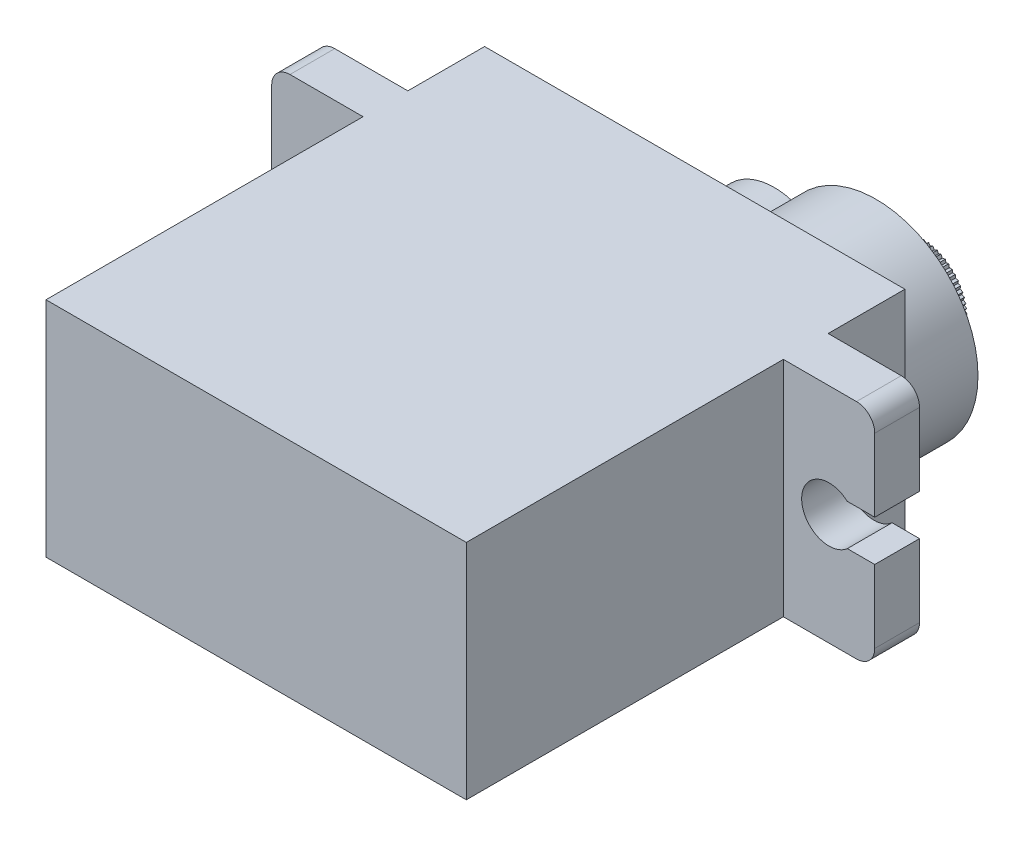
SolidWorks part; units mm, degrees
other "İşaretleme1"
sketch "Çizim23" plane through (16.5, -6.05, -13.15) normal (0.0047, -0.3236, -0.9462) x (-0.9915, -0.1242, 0.0376)
ref_plane "Ön Düzlem" through (0, 0, 0) normal (0, 0, 1) x (1, 0, 0)
ref_plane "Üst Düzlem" through (0, 0, 0) normal (0, 1, 0) x (1, 0, 0)
ref_plane "Sağ Düzlem" through (0, 0, 0) normal (1, 0, 0) x (0, 0, -1)
sketch "Çizim1" plane through (0, 0, 0) normal (0, 0, 1) x (1, 0, 0)
  line L1 (-11.5, -6.1) -> (11.5, -6.1)
  line L2 (-11.5, -6.1) -> (-11.5, 6.1)
  line L3 (-11.5, 6.1) -> (11.5, 6.1)
  line L4 (11.5, -6.1) -> (11.5, 6.1)
  line L5 (-11.5, -6.1) -> (11.5, 6.1) construction
  line L6 (-11.5, 6.1) -> (11.5, -6.1) construction
  point P0 (0, 0)
  dimension "D1" = 23
  dimension "D2" = 12.2
extrude "Yükseklik-Ekstrüzyon1" add sketch "Çizim1" along normal blind 17.35
sketch "Çizim4" plane through (11.5, 0, 0) normal (1, 0, 0) x (0, 0, -1)
  line L0 (-17.35, -6.1) -> (0, -6.1) construction
  line L1 (0, 6.1) -> (2.45, 6.1)
  line L2 (0, 6.1) -> (0, -6.1)
  line L3 (0, -6.1) -> (2.45, -6.1)
  line L4 (2.45, 6.1) -> (2.45, -6.1)
  dimension "D1" = 2.45
extrude "Yükseklik-Ekstrüzyon2" add sketch "Çizim4" along normal blind 5
sketch "Çizim5" plane through (-11.5, 0, 0) normal (-1, 0, 0) x (0, 0, 1)
  line L0 (17.35, 6.1) -> (0, 6.1) construction
  line L1 (0, -6.1) -> (-2.45, -6.1)
  line L2 (0, -6.1) -> (0, 6.1)
  line L3 (0, 6.1) -> (-2.45, 6.1)
  line L4 (-2.45, -6.1) -> (-2.45, 6.1)
  dimension "D1" = 2.45
extrude "Yükseklik-Ekstrüzyon3" add sketch "Çizim5" along normal blind 5
sketch "Çizim6" plane through (16.5, 0, 0) normal (1, 0, 0) x (0, 0, -1)
  line L0 (0, 0) -> (2.45, 0) construction
  line L1 (0, 6.1) -> (0, -6.1) construction
  line L2 (2.45, -6.1) -> (2.45, 6.1) construction
  line L4 (2.45, 1.12) -> (0, 1.12)
  line L5 (2.45, 1.12) -> (2.45, -1.12)
  line L6 (2.45, -1.12) -> (0, -1.12)
  line L7 (0, 1.12) -> (0, -1.12)
  line L8 (2.45, 1.12) -> (0, -1.12) construction
  line L9 (2.45, -1.12) -> (0, 1.12) construction
  point P6 (1.225, 0)
  dimension "D1" = 2.24
sketch "Çizim7" plane through (0, 0, 0) normal (0, 0, -1) x (-1, 0, 0)
  line L0 (-11.5, 6.1) -> (11.5, 6.1) construction
  line L1 (-11.5, -6.1) -> (11.5, -6.1)
  line L2 (-11.5, -6.1) -> (-11.5, 6.1)
  line L3 (-11.5, 6.1) -> (11.5, 6.1)
  line L4 (11.5, -6.1) -> (11.5, 6.1)
  line L5 (-11.5, -6.1) -> (11.5, 6.1) construction
  line L6 (-11.5, 6.1) -> (11.5, -6.1) construction
  point P0 (0, 0)
  dimension "D1" = 23
extrude "Yükseklik-Ekstrüzyon4" add sketch "Çizim7" along normal blind 6.65
sketch "Çizim8" plane through (0, 0, -2.45) normal (0, 0, -1) x (-1, 0, 0)
  line L0 (0, 0.2404) -> (0, 3.5063) construction
  circle A0 centre (-14, 0) radius 1.5
  circle A1 centre (14, 0) radius 1.5
  dimension "D2" = 3
  dimension "D1" = 2.5
extrude "Kes-Ekstrüzyon1" cut sketch "Çizim8" against normal up to surface (2.45 mm away) up to face at (14, 0, 0)
fillet "Radyus1" radius 1 4 edges at (-16.5, 6.1, -1.225) (-16.5, -6.1, -1.225) (16.5, -6.1, -1.225) (16.5, 6.1, -1.225)
extrude "Kes-Ekstrüzyon2" cut sketch "Çizim6" against normal up to surface (1.5022 mm away)
sketch "Çizim9" plane through (-16.5, 0, 0) normal (-1, 0, 0) x (0, 0, 1)
  line L0 (0, 0) -> (-2.45, 0) construction
  line L1 (-2.45, 6.1) -> (-2.45, -6.1) construction
  line L2 (0, -6.1) -> (0, 6.1) construction
  line L3 (-2.45, -1.12) -> (0, -1.12)
  line L4 (-2.45, -1.12) -> (-2.45, 1.12)
  line L5 (-2.45, 1.12) -> (0, 1.12)
  line L6 (0, -1.12) -> (0, 1.12)
  line L7 (-2.45, -1.12) -> (0, 1.12) construction
  line L8 (-2.45, 1.12) -> (0, -1.12) construction
  point P5 (-1.225, 0)
  dimension "D1" = 2.24
extrude "Kes-Ekstrüzyon3" cut sketch "Çizim9" against normal up to surface (1.5022 mm away)
sketch "Çizim10" plane through (0, 0, -6.65) normal (0, 0, -1) x (-1, 0, 0)
  line L0 (-11.5, 0) -> (-5.925, 0) construction
  line L1 (-11.5, 6.1) -> (-11.5, -6.1) construction
  circle A0 centre (-5.925, 0) radius 5.575
  dimension "D2" = 11.15
  dimension "D1" = 5.575
extrude "Yükseklik-Ekstrüzyon5" add sketch "Çizim10" along normal blind 4
sketch "Çizim11" plane through (0, 0, -10.65) normal (0, 0, -1) x (-1, 0, 0)
  circle A0 centre (-5.925, 0) radius 2.5
  dimension "D1" = 5
extrude "Yükseklik-Ekstrüzyon6" add sketch "Çizim11" along normal blind 2.5
sketch "Çizim12" plane through (0, 0, -6.65) normal (0, 0, -1) x (-1, 0, 0)
  line L0 (-0.35, 0) -> (3, 0) construction
  circle A0 centre (-5.925, 0) radius 5.575 construction
  circle A1 centre (-5.925, 0) radius 5.575 construction
  circle A2 centre (-0.35, 0) radius 3.35
  dimension "D1" = 3.35
extrude "Yükseklik-Ekstrüzyon7" add sketch "Çizim12" along normal blind 4
sketch "Çizim13" plane through (0, 0, -13.15) normal (0, 0, -1) x (-1, 0, 0)
  line L0 (-5.925, 2.375) -> (-5.815, 2.485)
  line L1 (-5.925, 2.375) -> (-6.035, 2.485)
  line L2 (-6.035, 2.485) -> (-6.1562, 2.3637)
  line L3 (-5.815, 2.485) -> (-5.6938, 2.3637)
  line L4 (-5.5481, 2.4587) -> (-5.6906, 2.3634)
  line L5 (-5.4617, 2.3294) -> (-5.5481, 2.4587)
  line L6 (-5.4617, 2.3294) -> (-5.3324, 2.4158)
  line L7 (-5.3324, 2.4158) -> (-5.2371, 2.2732)
  line L8 (-5.0756, 2.3379) -> (-5.234, 2.2723)
  line L9 (-5.0161, 2.1942) -> (-5.0756, 2.3379)
  line L10 (-5.0161, 2.1942) -> (-4.8725, 2.2537)
  line L11 (-4.8725, 2.2537) -> (-4.8068, 2.0953)
  line L12 (-4.6359, 2.1273) -> (-4.804, 2.0938)
  line L13 (-4.6055, 1.9747) -> (-4.6359, 2.1273)
  line L14 (-4.6055, 1.9747) -> (-4.453, 2.0051)
  line L15 (-4.453, 2.0051) -> (-4.4196, 1.8369)
  line L16 (-4.2456, 1.8349) -> (-4.4171, 1.8349)
  line L17 (-4.2456, 1.6794) -> (-4.2456, 1.8349)
  line L18 (-4.2456, 1.6794) -> (-4.0901, 1.6794)
  line L19 (-4.0901, 1.6794) -> (-4.0901, 1.5079)
  line L20 (-3.9199, 1.472) -> (-4.0881, 1.5054)
  line L21 (-3.9503, 1.3195) -> (-3.9199, 1.472)
  line L22 (-3.9503, 1.3195) -> (-3.7977, 1.2891)
  line L23 (-3.7977, 1.2891) -> (-3.8312, 1.121)
  line L24 (-3.6713, 1.0525) -> (-3.8297, 1.1182)
  line L25 (-3.7308, 0.9089) -> (-3.6713, 1.0525)
  line L26 (-3.7308, 0.9089) -> (-3.5871, 0.8494)
  line L27 (-3.5871, 0.8494) -> (-3.6527, 0.691)
  line L28 (-3.5092, 0.5926) -> (-3.6518, 0.6879)
  line L29 (-3.5956, 0.4633) -> (-3.5092, 0.5926)
  line L30 (-3.5956, 0.4633) -> (-3.4663, 0.3769)
  line L31 (-3.4663, 0.3769) -> (-3.5616, 0.2344)
  line L32 (-3.44, 0.11) -> (-3.5613, 0.2312)
  line L33 (-3.55, 0) -> (-3.44, 0.11)
  line L34 (-3.55, 0) -> (-3.44, -0.11)
  line L35 (-3.44, -0.11) -> (-3.5613, -0.2312)
  line L36 (-3.4663, -0.3769) -> (-3.5616, -0.2344)
  line L37 (-3.5956, -0.4633) -> (-3.4663, -0.3769)
  line L38 (-3.5956, -0.4633) -> (-3.5092, -0.5926)
  line L39 (-3.5092, -0.5926) -> (-3.6518, -0.6879)
  line L40 (-3.5871, -0.8494) -> (-3.6527, -0.691)
  line L41 (-3.7308, -0.9089) -> (-3.5871, -0.8494)
  line L42 (-3.7308, -0.9089) -> (-3.6713, -1.0525)
  line L43 (-3.6713, -1.0525) -> (-3.8297, -1.1182)
  line L44 (-3.7977, -1.2891) -> (-3.8312, -1.121)
  line L45 (-3.9503, -1.3195) -> (-3.7977, -1.2891)
  line L46 (-3.9503, -1.3195) -> (-3.9199, -1.472)
  line L47 (-3.9199, -1.472) -> (-4.0881, -1.5054)
  line L48 (-4.0901, -1.6794) -> (-4.0901, -1.5079)
  line L49 (-4.2456, -1.6794) -> (-4.0901, -1.6794)
  line L50 (-4.2456, -1.6794) -> (-4.2456, -1.8349)
  line L51 (-4.2456, -1.8349) -> (-4.4171, -1.8349)
  line L52 (-4.453, -2.0051) -> (-4.4196, -1.8369)
  line L53 (-4.6055, -1.9747) -> (-4.453, -2.0051)
  line L54 (-4.6055, -1.9747) -> (-4.6359, -2.1273)
  line L55 (-4.6359, -2.1273) -> (-4.804, -2.0938)
  line L56 (-4.8725, -2.2537) -> (-4.8068, -2.0953)
  line L57 (-5.0161, -2.1942) -> (-4.8725, -2.2537)
  line L58 (-5.0161, -2.1942) -> (-5.0756, -2.3379)
  line L59 (-5.0756, -2.3379) -> (-5.234, -2.2723)
  line L60 (-5.3324, -2.4158) -> (-5.2371, -2.2732)
  line L61 (-5.4617, -2.3294) -> (-5.3324, -2.4158)
  line L62 (-5.4617, -2.3294) -> (-5.5481, -2.4587)
  line L63 (-5.5481, -2.4587) -> (-5.6906, -2.3634)
  line L64 (-5.815, -2.485) -> (-5.6938, -2.3637)
  line L65 (-5.925, -2.375) -> (-5.815, -2.485)
  line L66 (-5.925, -2.375) -> (-6.035, -2.485)
  line L67 (-6.035, -2.485) -> (-6.1562, -2.3637)
  line L68 (-6.3019, -2.4587) -> (-6.1594, -2.3634)
  line L69 (-6.3883, -2.3294) -> (-6.3019, -2.4587)
  line L70 (-6.3883, -2.3294) -> (-6.5176, -2.4158)
  line L71 (-6.5176, -2.4158) -> (-6.6129, -2.2732)
  line L72 (-6.7744, -2.3379) -> (-6.616, -2.2723)
  line L73 (-6.8339, -2.1942) -> (-6.7744, -2.3379)
  line L74 (-6.8339, -2.1942) -> (-6.9775, -2.2537)
  line L75 (-6.9775, -2.2537) -> (-7.0432, -2.0953)
  line L76 (-7.2141, -2.1273) -> (-7.046, -2.0938)
  line L77 (-7.2445, -1.9747) -> (-7.2141, -2.1273)
  line L78 (-7.2445, -1.9747) -> (-7.397, -2.0051)
  line L79 (-7.397, -2.0051) -> (-7.4304, -1.8369)
  line L80 (-7.6044, -1.8349) -> (-7.4329, -1.8349)
  line L81 (-7.6044, -1.6794) -> (-7.6044, -1.8349)
  line L82 (-7.6044, -1.6794) -> (-7.7599, -1.6794)
  line L83 (-7.7599, -1.6794) -> (-7.7599, -1.5079)
  line L84 (-7.9301, -1.472) -> (-7.7619, -1.5054)
  line L85 (-7.8997, -1.3195) -> (-7.9301, -1.472)
  line L86 (-7.8997, -1.3195) -> (-8.0523, -1.2891)
  line L87 (-8.0523, -1.2891) -> (-8.0188, -1.121)
  line L88 (-8.1787, -1.0525) -> (-8.0203, -1.1182)
  line L89 (-8.1192, -0.9089) -> (-8.1787, -1.0525)
  line L90 (-8.1192, -0.9089) -> (-8.2629, -0.8494)
  line L91 (-8.2629, -0.8494) -> (-8.1973, -0.691)
  line L92 (-8.3408, -0.5926) -> (-8.1982, -0.6879)
  line L93 (-8.2544, -0.4633) -> (-8.3408, -0.5926)
  line L94 (-8.2544, -0.4633) -> (-8.3837, -0.3769)
  line L95 (-8.3837, -0.3769) -> (-8.2884, -0.2344)
  line L96 (-8.41, -0.11) -> (-8.2887, -0.2312)
  line L97 (-8.3, 0) -> (-8.41, -0.11)
  line L98 (-8.3, 0) -> (-8.41, 0.11)
  line L99 (-8.41, 0.11) -> (-8.2887, 0.2312)
  line L100 (-8.3837, 0.3769) -> (-8.2884, 0.2344)
  line L101 (-8.2544, 0.4633) -> (-8.3837, 0.3769)
  line L102 (-8.2544, 0.4633) -> (-8.3408, 0.5926)
  line L103 (-8.3408, 0.5926) -> (-8.1982, 0.6879)
  line L104 (-8.2629, 0.8494) -> (-8.1973, 0.691)
  line L105 (-8.1192, 0.9089) -> (-8.2629, 0.8494)
  line L106 (-8.1192, 0.9089) -> (-8.1787, 1.0525)
  line L107 (-8.1787, 1.0525) -> (-8.0203, 1.1182)
  line L108 (-8.0523, 1.2891) -> (-8.0188, 1.121)
  line L109 (-7.8997, 1.3195) -> (-8.0523, 1.2891)
  line L110 (-7.8997, 1.3195) -> (-7.9301, 1.472)
  line L111 (-7.9301, 1.472) -> (-7.7619, 1.5054)
  line L112 (-7.7599, 1.6794) -> (-7.7599, 1.5079)
  line L113 (-7.6044, 1.6794) -> (-7.7599, 1.6794)
  line L114 (-7.6044, 1.6794) -> (-7.6044, 1.8349)
  line L115 (-7.6044, 1.8349) -> (-7.4329, 1.8349)
  line L116 (-7.397, 2.0051) -> (-7.4304, 1.8369)
  line L117 (-7.2445, 1.9747) -> (-7.397, 2.0051)
  line L118 (-7.2445, 1.9747) -> (-7.2141, 2.1273)
  line L119 (-7.2141, 2.1273) -> (-7.046, 2.0938)
  line L120 (-6.9775, 2.2537) -> (-7.0432, 2.0953)
  line L121 (-6.8339, 2.1942) -> (-6.9775, 2.2537)
  line L122 (-6.8339, 2.1942) -> (-6.7744, 2.3379)
  line L123 (-6.7744, 2.3379) -> (-6.616, 2.2723)
  line L124 (-6.5176, 2.4158) -> (-6.6129, 2.2732)
  line L125 (-6.3883, 2.3294) -> (-6.5176, 2.4158)
  line L126 (-6.3883, 2.3294) -> (-6.3019, 2.4587)
  line L127 (-6.3019, 2.4587) -> (-6.1594, 2.3634)
  line L128 (-8.1973, 0.691) -> (-8.1982, 0.6879)
  line L129 (-8.0188, 1.121) -> (-8.0203, 1.1182)
  line L130 (-7.7599, 1.5079) -> (-7.7619, 1.5054)
  line L131 (-7.4304, 1.8369) -> (-7.4329, 1.8349)
  line L132 (-7.0432, 2.0953) -> (-7.046, 2.0938)
  line L133 (-6.6129, 2.2732) -> (-6.616, 2.2723)
  line L134 (-6.1562, 2.3637) -> (-6.1594, 2.3634)
  line L135 (-5.6906, 2.3634) -> (-5.6938, 2.3637)
  line L136 (-5.234, 2.2723) -> (-5.2371, 2.2732)
  line L137 (-4.804, 2.0938) -> (-4.8068, 2.0953)
  line L138 (-4.4171, 1.8349) -> (-4.4196, 1.8369)
  line L139 (-4.0881, 1.5054) -> (-4.0901, 1.5079)
  line L140 (-3.8297, 1.1182) -> (-3.8312, 1.121)
  line L141 (-3.6518, 0.6879) -> (-3.6527, 0.691)
  line L142 (-3.5613, 0.2312) -> (-3.5616, 0.2344)
  line L143 (-3.5616, -0.2344) -> (-3.5613, -0.2312)
  line L144 (-3.6527, -0.691) -> (-3.6518, -0.6879)
  line L145 (-3.8312, -1.121) -> (-3.8297, -1.1182)
  line L146 (-4.0901, -1.5079) -> (-4.0881, -1.5054)
  line L147 (-4.4196, -1.8369) -> (-4.4171, -1.8349)
  line L148 (-4.8068, -2.0953) -> (-4.804, -2.0938)
  line L149 (-5.2371, -2.2732) -> (-5.234, -2.2723)
  line L150 (-5.6938, -2.3637) -> (-5.6906, -2.3634)
  line L151 (-6.1594, -2.3634) -> (-6.1562, -2.3637)
  line L152 (-6.616, -2.2723) -> (-6.6129, -2.2732)
  line L153 (-7.046, -2.0938) -> (-7.0432, -2.0953)
  line L154 (-7.4329, -1.8349) -> (-7.4304, -1.8369)
  line L155 (-7.7619, -1.5054) -> (-7.7599, -1.5079)
  line L156 (-8.0203, -1.1182) -> (-8.0188, -1.121)
  line L157 (-8.1982, -0.6879) -> (-8.1973, -0.691)
  line L158 (-8.2887, -0.2312) -> (-8.2884, -0.2344)
  line L159 (-8.2884, 0.2344) -> (-8.2887, 0.2312)
  circle A1 centre (-5.925, 0) radius 2.5
  point P167 (-5.925, 0)
  point P229 (-5.925, 0)
  dimension "D1" = 32
  dimension "D2" = 32
extrude "Kes-Ekstrüzyon4" cut sketch "Çizim13" against normal up to surface (2.5 mm away) up to face at (3.425, 0, -10.65)
sketch "Çizim14" plane through (0, 0, -13.15) normal (0, 0, -1) x (-1, 0, 0)
  line L0 (-11.5, 0) -> (-5.925, 0) construction
  line L1 (-11.5, -6.1) -> (-11.5, 6.1) construction
  circle A0 centre (-5.925, 0) radius 0.75
  dimension "D1" = 1.5
extrude "Kes-Ekstrüzyon5" cut sketch "Çizim14" against normal blind 1
sketch "Çizim15" plane through (0, -6.1, 0) normal (0, -1, 0) x (1, 0, 0)
  line L0 (0, 17.35) -> (0, 15.35) construction
  line L1 (-11.5, 17.35) -> (11.5, 17.35) construction
  line L2 (-11.5, 8.675) -> (-9.5, 8.675) construction
  line L3 (-11.5, 17.35) -> (-11.5, 0) construction
  line L4 (11.5, 17.35) -> (11.5, 0) construction
  line L5 (-9.5, 15.35) -> (9.5, 15.35)
  line L6 (-9.5, 15.35) -> (-9.5, 2)
  line L7 (-9.5, 2) -> (9.5, 2)
  line L8 (9.5, 15.35) -> (9.5, 2)
  dimension "D1" = 2
  dimension "D2" = 2
  dimension "D3" = 2
  dimension "D4" = 2
  dimension "D5" = 2
extrude "Yükseklik-Ekstrüzyon8" add sketch "Çizim15" along normal blind 0.1
sketch "Çizim17" plane through (0, -6.2, 0) normal (0, -1, 0) x (1, 0, 0)
  line L0 (-9.5, 8.675) -> (9.5, 8.675) construction
  line L1 (-9.5, 15.35) -> (-9.5, 2) construction
  line L2 (9.5, 2) -> (9.5, 15.35) construction
  line L4 (-9.5, 6.925) -> (9.5, 6.925)
  line L5 (-9.5, 6.925) -> (-9.5, 10.425)
  line L6 (-9.5, 10.425) -> (9.5, 10.425)
  line L7 (9.5, 6.925) -> (9.5, 10.425)
  line L8 (-9.5, 6.925) -> (9.5, 10.425) construction
  line L9 (-9.5, 10.425) -> (9.5, 6.925) construction
  point P6 (0, 8.675)
  dimension "D1" = 3.5
extrude "Yükseklik-Ekstrüzyon9" add sketch "Çizim17" along normal blind 0.05
sketch "Çizim18" plane through (0, -6.25, 0) normal (0, -1, 0) x (1, 0, 0)
  line L0 (-9.5, 9.425) -> (9.5, 9.425) construction
  line L2 (9.5, 6.925) -> (9.5, 10.425) construction
  line L3 (9.5, 9.425) -> (9.5, 10.425) construction
  line L4 (9.5, 2) -> (9.5, 15.35) construction
  line L7 (-9.5, 15.35) -> (-9.5, 2) construction
  text T0 "MG90S" font "Century Gothic" height 1.5
extrude "Kes-Ekstrüzyon7" cut sketch "Çizim18" against normal blind 0.05
sketch "Çizim19" plane through (0, -6.2, 0) normal (0, -1, 0) x (1, 0, 0)
  line L0 (9.5, 12.8875) -> (-9.5, 12.8875) construction
  line L1 (9.5, 10.425) -> (9.5, 15.35) construction
  line L2 (-9.5, 15.35) -> (-9.5, 10.425) construction
  text T0 "MİCRO SERVO" font "Century Gothic" height 1.5
extrude "Kes-Ekstrüzyon8" cut sketch "Çizim19" against normal blind 0.1
sketch "Çizim21" plane through (0, -6.1, 0) normal (0, -1, 0) x (1, 0, 0)
  line L11 (-9.5, 2) -> (9.5, 2) construction
  line L12 (9.5, 2) -> (9.5, 15.35) construction
  line L13 (-9.5, 15.35) -> (-9.5, 2) construction
  line L14 (9.5, 15.35) -> (-9.5, 15.35) construction
  line L15 (-9.75, 1.75) -> (9.75, 1.75)
  line L16 (9.75, 1.75) -> (9.75, 15.6)
  line L17 (-9.75, 15.6) -> (-9.75, 1.75)
  line L18 (9.75, 15.6) -> (-9.75, 15.6)
  line L19 (-9.75, 1.75) -> (9.75, 1.75)
  line L20 (9.75, 1.75) -> (9.75, 15.6)
  line L21 (-9.75, 15.6) -> (-9.75, 1.75)
  line L22 (9.75, 15.6) -> (-9.75, 15.6)
  line L23 (-9.5, 2) -> (9.5, 2)
  line L24 (9.5, 2) -> (9.5, 15.35)
  line L25 (-9.5, 15.35) -> (-9.5, 2)
  line L26 (9.5, 15.35) -> (-9.5, 15.35)
  dimension "D1" = 0.25
extrude "Yükseklik-Ekstrüzyon10" add sketch "Çizim21" along normal blind 0.11
sketch "Çizim22" plane through (0, -6.1, 0) normal (0, -1, 0) x (1, 0, 0)
  line L0 (-9.75, 1.75) -> (9.75, 1.75) construction
  line L1 (9.75, 1.75) -> (9.75, 15.6) construction
  line L2 (9.75, 15.6) -> (-9.75, 15.6) construction
  line L3 (-9.75, 15.6) -> (-9.75, 1.75) construction
  line L4 (-9.75, 1.75) -> (9.75, 1.75)
  line L5 (9.75, 1.75) -> (9.75, 15.6)
  line L6 (9.75, 15.6) -> (-9.75, 15.6)
  line L7 (-9.75, 15.6) -> (-9.75, 1.75)
  line L8 (10, 15.85) -> (-10, 15.85)
  line L9 (-10, 15.85) -> (-10, 1.5)
  line L10 (-10, 1.5) -> (10, 1.5)
  line L11 (10, 1.5) -> (10, 15.85)
  dimension "D1" = 0.25
extrude "Yükseklik-Ekstrüzyon11" add sketch "Çizim22" along normal blind 0.1
